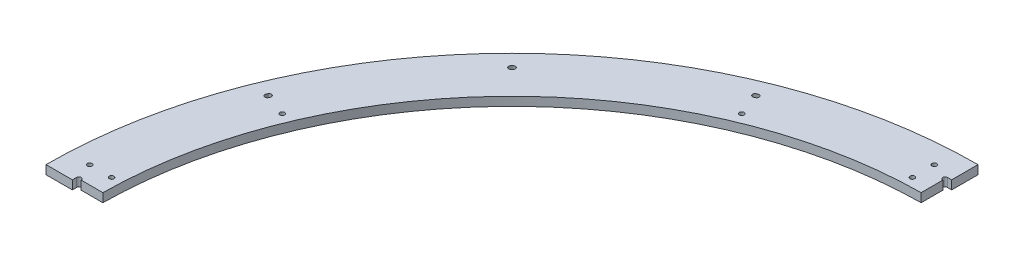
SolidWorks part; units mm, degrees
material "PE High Density"
ref_plane "Front Plane" through (0, 0, 0) normal (0, 0, 1) x (1, 0, 0)
ref_plane "Top Plane" through (0, 0, 0) normal (0, 1, 0) x (1, 0, 0)
ref_plane "Right Plane" through (0, 0, 0) normal (1, 0, 0) x (0, 0, -1)
sketch "Sketch1" plane through (0, 0, 0) normal (0, 1, 0) x (1, 0, 0)
  line L0 (-598.4875, 0) -> (-674.6875, 0)
  line L1 (598.4875, 0) -> (674.6875, 0)
  arc A0 (-598.4875, 0) -> (598.4875, 0) centre (0, 0) cw
  arc A1 (-674.6875, 0) -> (674.6875, 0) centre (0, 0) cw
  dimension "D2" = 598.4875
  dimension "D1" = 76.2
extrude "Boss-Extrude1" add sketch "Sketch1" along normal blind 12.7
sketch "Sketch2" plane through (0, 12.7, 0) normal (0, 1, 0) x (1, 0, 0)
  line L1 (-6.35, 598.4538) -> (6.35, 598.4538)
  line L2 (-6.35, 598.4538) -> (-6.35, 636.5875)
  line L3 (-6.35, 636.5875) -> (6.35, 636.5875)
  line L4 (6.35, 598.4538) -> (6.35, 636.5875)
  line L8 (598.4538, 6.35) -> (636.5875, 6.35)
  line L9 (0, 0) -> (0, 598.4538) construction
  line L14 (0, 674.6875) -> (0, 598.4875) construction
  line L15 (598.4538, 6.35) -> (598.4538, -6.35)
  line L16 (598.4538, -6.35) -> (636.5875, -6.35)
  line L17 (636.5875, 6.35) -> (636.5875, -6.35)
  line L18 (6.35, -598.4538) -> (6.35, -636.5875)
  line L19 (6.35, -598.4538) -> (-6.35, -598.4538)
  line L20 (-6.35, -598.4538) -> (-6.35, -636.5875)
  line L21 (6.35, -636.5875) -> (-6.35, -636.5875)
  line L22 (-598.4538, -6.35) -> (-636.5875, -6.35)
  line L23 (-598.4538, -6.35) -> (-598.4538, 6.35)
  line L24 (-598.4538, 6.35) -> (-636.5875, 6.35)
  line L25 (-636.5875, -6.35) -> (-636.5875, 6.35)
  line L26 (598.4875, 0) -> (674.6875, 0) construction
  arc A0 (598.4875, 0) -> (-598.4875, 0) centre (0, 0) ccw construction
  arc A1 (674.6875, 0) -> (-674.6875, 0) centre (0, 0) ccw construction
  point P7 (0, 598.4538)
  point P16 (0, 0)
  point P23 (0, 636.5875)
  point P33 (0, 0)
  dimension "D1" = 38.1
  dimension "D2" = 12.7
  dimension "D3" = 4
extrude "Cut-Extrude1" cut sketch "Sketch2" against normal through all
sketch "Sketch3" plane through (0, 12.7, 0) normal (0, 1, 0) x (1, 0, 0)
  line L0 (-6.35, 636.5875) -> (-6.35, 633.1585) construction
  line L1 (6.35, 636.5875) -> (-6.35, 636.5875) construction
  line L2 (0, 636.5875) -> (0, 0) construction
  line L3 (-636.5875, 6.35) -> (-633.1585, 6.35) construction
  line L5 (-6.35, 636.5875) -> (-6.35, 598.4538) construction
  line L6 (-598.4538, 6.35) -> (-636.5875, 6.35) construction
  circle A0 centre (-6.35, 633.1585) radius 3.429
  circle A1 centre (-633.1585, 6.35) radius 3.429
  circle A2 centre (6.35, 633.1585) radius 3.429
  circle A3 centre (633.1585, 6.35) radius 3.429
  dimension "D1" = 6.858
extrude "Cut-Extrude2" cut sketch "Sketch3" against normal through all contours A1 | A0 | A2 | A3
hole_wizard "1/4 Clearance Hole2" positions "Sketch6" profile "Sketch7" hole size "1/4" standard "ANSI Inch" end condition through all
sketch "Sketch6" plane through (0, 12.7, 0) normal (0, 1, 0) x (1, 0, 0)
  line L0 (0, 636.5875) -> (0, 598.4875) construction
  line L1 (6.35, 636.5875) -> (-6.35, 636.5875) construction
  line L2 (-6.35, 629.7295) -> (-6.35, 598.4538) construction
  line L3 (-636.5875, 0) -> (-598.4875, 0) construction
  line L4 (-31.75, 642.9375) -> (-31.75, 611.1875) construction
  line L5 (-31.75, 611.1875) -> (-31.75, 598.4875) construction
  line L6 (-31.75, 598.4875) -> (0, 598.4875) construction
  line L8 (-598.4875, 0) -> (-598.4875, 31.75) construction
  line L9 (-598.4875, 31.75) -> (-611.1875, 31.75) construction
  line L10 (-611.1875, 31.75) -> (-642.9375, 31.75) construction
  line L11 (-598.4875, 0) -> (-552.9304, 229.0313) construction
  line L12 (-552.9304, 229.0313) -> (-423.1946, 423.1946) construction
  line L13 (-423.1946, 423.1946) -> (0, 0) construction
  line L15 (-552.9304, 229.0313) -> (-567.5969, 235.1064) construction
  arc A0 (-6.35, 598.4538) -> (-598.4538, 6.35) centre (0, 0) ccw construction
  point P0 (-31.75, 642.9375)
  point P2 (-31.75, 611.1875)
  point P39 (-611.1875, 31.75)
  point P42 (-642.9375, 31.75)
  point P62 (-567.5969, 235.1064)
  point P70 (-235.1064, 567.5969)
  dimension "D1" = 38.1
  dimension "D2" = 25.4
  dimension "D3" = 12.7
  dimension "D4" = 31.75
  dimension "D5" = 15.875
sketch "Sketch7" plane through (-31.75, 12.7, -642.9375) normal (1, 0, 0) x (0, 0, 1)
  line L0 (0, 0) -> (0, 12.7)
  line L1 (0, 12.7) -> (3.3782, 12.7)
  line L2 (3.3782, 12.7) -> (3.3782, 0)
  line L5 (3.3782, 0) -> (0, 0)
  line L11 (0, -6.35) -> (0, 107.95) construction
  dimension "Thru Hole Dia." = 6.7564
  dimension "Thru Hole Depth" = 12.7
sketch "Sketch8" plane through (0, 12.7, 0) normal (0, 1, 0) x (1, 0, 0)
  line L1 (674.6875, 0) -> (0, 0)
  line L2 (674.6875, 0) -> (674.6875, 674.6875)
  line L3 (674.6875, 674.6875) -> (0, 674.6875)
  line L4 (0, 0) -> (0, 674.6875)
  arc A0 (674.6875, 0) -> (-674.6875, 0) centre (0, 0) ccw construction
extrude "Cut-Extrude4" cut sketch "Sketch8" against normal through all
sketch "Sketch10" plane through (0, 12.7, 0) normal (0, 1, 0) x (1, 0, 0)
  line L1 (0, 674.6875) -> (-0.3175, 674.6875)
  line L2 (0, 674.6875) -> (0, 636.5875)
  line L3 (0, 636.5875) -> (-0.3175, 636.5875)
  line L4 (-0.3175, 674.6875) -> (-0.3175, 636.5875)
  line L5 (0, 636.5875) -> (-6.35, 636.5875) construction
  line L6 (0, 0) -> (-477.0761, 477.0761) construction
  line L7 (-674.6875, 0.3175) -> (-636.5875, 0.3175)
  line L8 (-636.5875, 0) -> (-636.5875, 0.3175)
  line L9 (-674.6875, 0) -> (-636.5875, 0)
  line L10 (-674.6875, 0) -> (-674.6875, 0.3175)
  arc A0 (0, 674.6875) -> (-674.6875, 0) centre (0, 0) ccw construction
  dimension "D1" = 0.3175
extrude "Cut-Extrude5" cut sketch "Sketch10" against normal through all
fillet "Fillet1" [suppressed] radius 0.762
hole_wizard "1/4 Clearance Hole1" [suppressed] positions "Sketch11" profile "Sketch12" hole size "1/4" standard "ANSI Inch"
sketch "Sketch11" plane through (0, 12.7, 0) normal (0, 1, 0) x (1, 0, 0)
  line L0 (0, 0) -> (-478.1986, 478.1986) construction
  line L1 (-625.2272, 257.7573) -> (0, 0) construction
  line L3 (-478.1986, 478.1986) -> (-479.3212, 479.3212) construction
  line L5 (-479.3212, 479.3212) -> (-480.6628, 480.6628) construction
  arc A1 (-0.3175, 674.6874) -> (-674.6874, 0.3175) centre (0, 0) ccw construction
  arc A2 (-478.1986, 478.1986) -> (-625.2272, 257.7573) centre (0, 0) ccw construction
  arc A3 (-459.1156, 459.1156) -> (-600.2768, 247.4712) centre (0, 0) ccw construction
  point P12 (-477.0761, 477.0761)
  point P16 (-459.1156, 459.1156)
  point P18 (-600.2768, 247.4712)
  point P46 (-247.4712, 600.2768)
  dimension "D2" = 266.7
  dimension "D1" = 1.5875
  dimension "D3" = 1.5875
  dimension "D4" = 1.8974
  dimension "D5" = 30.4724
  dimension "D6" = 25.4
sketch "Sketch12" plane through (-247.4712, 12.7, -600.2768) normal (1, 0, 0) x (0, 0, 1)
  line L0 (0, 0) -> (0, 12.7)
  line L1 (0, 12.7) -> (3.3782, 12.7)
  line L2 (3.3782, 12.7) -> (3.3782, 0)
  line L5 (3.3782, 0) -> (0, 0)
  line L11 (0, -6.35) -> (0, 107.95) construction
  dimension "Thru Hole Dia." = 6.7564
  dimension "Thru Hole Depth" = 12.7
sketch "Sketch13" plane through (0, 12.7, 0) normal (0, 1, 0) x (1, 0, 0)
  arc A0 (-600.6826, 246.4846) -> (-599.8694, 248.4571) centre (0, 0) cw construction
  arc A1 (-602.9905, 249.7498) -> (-603.8079, 247.767) centre (0, 0) ccw
  arc A2 (-596.7483, 247.1644) -> (-597.5573, 245.2021) centre (0, 0) ccw
  arc A3 (-596.7483, 247.1644) -> (-602.9905, 249.7498) centre (-599.8694, 248.4571) ccw
  arc A4 (-603.8079, 247.767) -> (-597.5573, 245.2021) centre (-600.6826, 246.4846) ccw
  arc A5 (-459.8693, 458.3606) -> (-458.3606, 459.8693) centre (0, 0) cw construction
  arc A6 (-459.1156, 459.1156) -> (-600.2768, 247.4712) centre (0, 0) ccw construction
  arc A7 (-460.7454, 462.262) -> (-462.262, 460.7454) centre (0, 0) ccw
  arc A8 (-455.9758, 457.4767) -> (-457.4767, 455.9758) centre (0, 0) ccw
  arc A9 (-455.9758, 457.4767) -> (-460.7454, 462.262) centre (-458.3606, 459.8693) ccw
  arc A10 (-462.262, 460.7454) -> (-457.4767, 455.9758) centre (-459.8693, 458.3606) ccw
  arc A11 (-248.4571, 599.8694) -> (-246.4846, 600.6826) centre (0, 0) cw construction
  arc A12 (-247.767, 603.8079) -> (-249.7498, 602.9905) centre (0, 0) ccw
  arc A13 (-245.2021, 597.5573) -> (-247.1644, 596.7483) centre (0, 0) ccw
  arc A14 (-245.2021, 597.5573) -> (-247.767, 603.8079) centre (-246.4846, 600.6826) ccw
  arc A15 (-249.7498, 602.9905) -> (-247.1644, 596.7483) centre (-248.4571, 599.8694) ccw
  point P4 (-600.2768, 247.4712)
  point P9 (-459.1156, 459.1156)
  point P20 (-247.4712, 600.2768)
  point P28 (-601.9569, 243.3559)
  point P38 (-598.5767, 251.5782)
  dimension "D3" = 649.2875
  dimension "D6" = 649.2875
  dimension "D9" = 649.2875
  dimension "D1" = 6.7564
  dimension "D4" = 6.7564
  dimension "D7" = 6.7564
  dimension "D10" = 8.89
  dimension "D2" = 0.188
  dimension "D5" = 0.188
  dimension "D8" = 0.188
extrude "Cut-Extrude6" cut sketch "Sketch13" against normal through all
